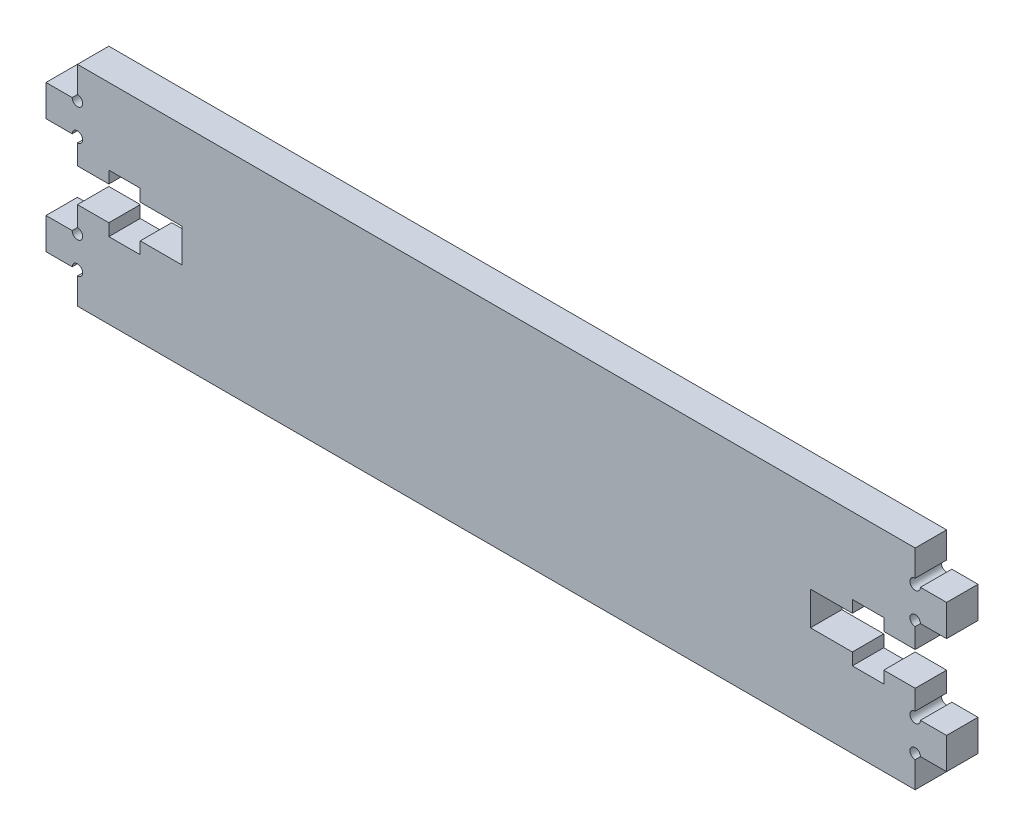
SolidWorks part; units mm, degrees
material "Acrylic (Medium-high impact)"
ref_plane "Front Plane" through (0, 0, 0) normal (0, 0, 1) x (1, 0, 0)
ref_plane "Top Plane" through (0, 0, 0) normal (0, 1, 0) x (1, 0, 0)
ref_plane "Right Plane" through (0, 0, 0) normal (1, 0, 0) x (0, 0, -1)
sketch "Sketch1" plane through (0, 0, 0) normal (0, 0, 1) x (1, 0, 0)
  line L1 (-47.0399, -15) -> (32.9601, -15)
  line L5 (-47.0399, 2) -> (-50.0399, 2)
  line L8 (-47.0399, -15) -> (-47.0399, 5)
  line L9 (32.9601, 5) -> (32.9601, -15)
  line L13 (-47.0399, 5) -> (32.9601, 5)
  line L15 (-50.0399, 2) -> (-50.0399, -1)
  line L16 (-50.0399, -1) -> (-47.0399, -1)
  line L17 (-47.0399, -9) -> (-50.0399, -9)
  line L18 (-50.0399, -9) -> (-50.0399, -12)
  line L19 (-50.0399, -12) -> (-47.0399, -12)
  line L20 (-47.0399, -3.4) -> (-44.0399, -3.4)
  line L21 (-44.0399, -3.4) -> (-44.0399, -2.25)
  line L22 (-44.0399, -2.25) -> (-41.0399, -2.25)
  line L23 (-41.0399, -2.25) -> (-41.0399, -3.4)
  line L24 (-41.0399, -3.4) -> (-37.0399, -3.4)
  line L25 (-37.0399, -3.4) -> (-37.0399, -6.6)
  line L26 (-37.0399, -6.6) -> (-41.0399, -6.6)
  line L27 (-41.0399, -6.6) -> (-41.0399, -7.75)
  line L28 (-41.0399, -7.75) -> (-44.0399, -7.75)
  line L29 (-44.0399, -7.75) -> (-44.0399, -6.6)
  line L30 (-44.0399, -6.6) -> (-47.0399, -6.6)
  line L31 (-7.0399, 5) -> (-7.0399, -15) construction
  line L32 (29.9601, -6.6) -> (32.9601, -6.6)
  line L33 (29.9601, -7.75) -> (29.9601, -6.6)
  line L34 (26.9601, -7.75) -> (29.9601, -7.75)
  line L35 (26.9601, -6.6) -> (26.9601, -7.75)
  line L36 (22.9601, -6.6) -> (26.9601, -6.6)
  line L37 (22.9601, -3.4) -> (22.9601, -6.6)
  line L38 (26.9601, -3.4) -> (22.9601, -3.4)
  line L39 (26.9601, -2.25) -> (26.9601, -3.4)
  line L40 (29.9601, -2.25) -> (26.9601, -2.25)
  line L41 (29.9601, -3.4) -> (29.9601, -2.25)
  line L42 (32.9601, -3.4) -> (29.9601, -3.4)
  line L43 (35.9601, -12) -> (32.9601, -12)
  line L44 (35.9601, -9) -> (35.9601, -12)
  line L45 (32.9601, -9) -> (35.9601, -9)
  line L46 (35.9601, -1) -> (32.9601, -1)
  line L47 (35.9601, 2) -> (35.9601, -1)
  line L48 (32.9601, 2) -> (35.9601, 2)
  point P0 (0, 0)
  point P16 (-45.5399, -6.6)
  dimension "D1" = 20
  dimension "D2" = 80
  dimension "D3" = 3.2
  dimension "D4" = 3
  dimension "D5" = 3
  dimension "D6" = 3
  dimension "D7" = 3
  dimension "D8" = 8
  dimension "D9" = 3
  dimension "D10" = 8.4
  dimension "D11" = 3
  dimension "D12" = 4
  dimension "D13" = 3
  dimension "D14" = 5.5
  dimension "D15" = 40
extrude "Boss-Extrude1" add sketch "Sketch1" along normal blind 3 contours L29 L30 L8 L1 L9 L13 L20 L21 L22 L23 L24 L25 L26 L27 L28 | L18 L19 L8 L17 | L15 L16 L8 L5 | L13 L31 L1 L9 L32 L33 L34 L35 L36 L37 L38 L39 L40 L41 L42 | L45 L9 L43 L44 | L48 L9 L46 L47
sketch "Sketch2" plane through (0, 0, 3) normal (0, 0, 1) x (1, 0, 0)
  circle A4 centre (-47.0399, 2) radius 0.5
  circle A5 centre (-47.0399, -1) radius 0.5
  circle A6 centre (-47.0399, -12) radius 0.5
  circle A7 centre (-47.0399, -9) radius 0.5
  circle A8 centre (32.9601, 2) radius 0.5
  circle A9 centre (32.9601, -1) radius 0.5
  circle A10 centre (32.9601, -9) radius 0.5
  circle A11 centre (32.9601, -12) radius 0.5
  dimension "D1" = 1
extrude "Cut-Extrude1" cut sketch "Sketch2" against normal through all
